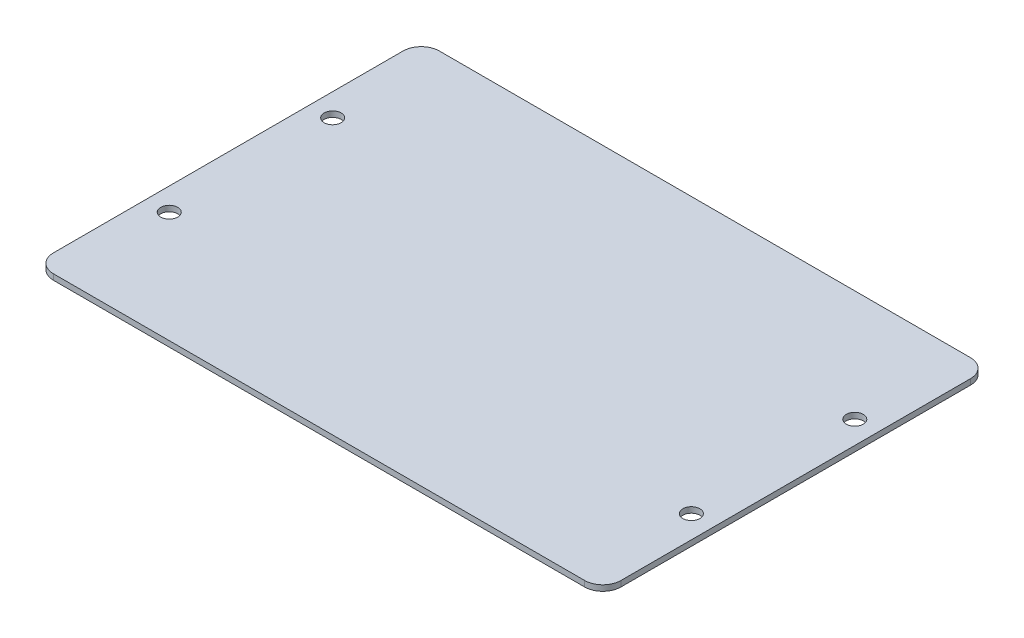
SolidWorks part; units mm, degrees
ref_plane "Front Plane" through (0, 0, 0) normal (0, 0, 1) x (1, 0, 0)
ref_plane "Top Plane" through (0, 0, 0) normal (0, 1, 0) x (1, 0, 0)
ref_plane "Right Plane" through (0, 0, 0) normal (1, 0, 0) x (0, 0, -1)
sketch "Sketch1" plane through (0, 0, 0) normal (0, 1, 0) x (1, 0, 0)
  line L0 (-125, -85) -> (125, 85) construction
  line L1 (-125, 85) -> (125, 85)
  line L2 (-125, 85) -> (-125, -85)
  line L3 (-125, -85) -> (125, -85)
  line L4 (125, 85) -> (125, -85)
  line L5 (125, -85) -> (-125, 85) construction
  point P4 (0, 0)
  dimension "D1" = 250
  dimension "D2" = 170
extrude "Boss-Extrude1" add sketch "Sketch1" along normal blind 2.5
sketch "Sketch2" plane through (0, 2.5, 0) normal (0, 1, 0) x (1, 0, 0)
  line L0 (-151.6898, 0) -> (155.8571, 0) construction
  line L1 (0, 100.2931) -> (0, -100.2931) construction
  line L2 (-125, 85) -> (-125, -85) construction
  circle A0 centre (-115, 36) radius 3.75
  circle A1 centre (-115, -36) radius 3.75
  circle A2 centre (115, -36) radius 3.75
  circle A3 centre (115, 36) radius 3.75
  point P15 (163.0804, -36)
  dimension "D1" = 7.5
  dimension "D2" = 72
  dimension "D3" = 10
extrude "Cut-Extrude1" cut sketch "Sketch2" against normal through all
fillet "Fillet1" radius 8 4 edges at (-125, 1.25, -85) (125, 1.25, -85) (125, 1.25, 85) (-125, 1.25, 85)
sketch "Sketch4" plane through (0, 0, 0) normal (0, -1, 0) x (1, 0, 0)
  line L0 (0, 51.6745) -> (0, -39.7283) construction
  line L1 (-20, 41) -> (20, 41)
  line L2 (-20, 41) -> (-20, -9)
  line L3 (-20, -9) -> (20, -9)
  line L4 (20, 41) -> (20, -9)
  line L5 (-117, 85) -> (117, 85) construction
  point P6 (0, 41)
  dimension "D1" = 40
  dimension "D2" = 50
  dimension "D3" = 44
extrude "Boss-Extrude2" add sketch "Sketch4" along normal blind 15
